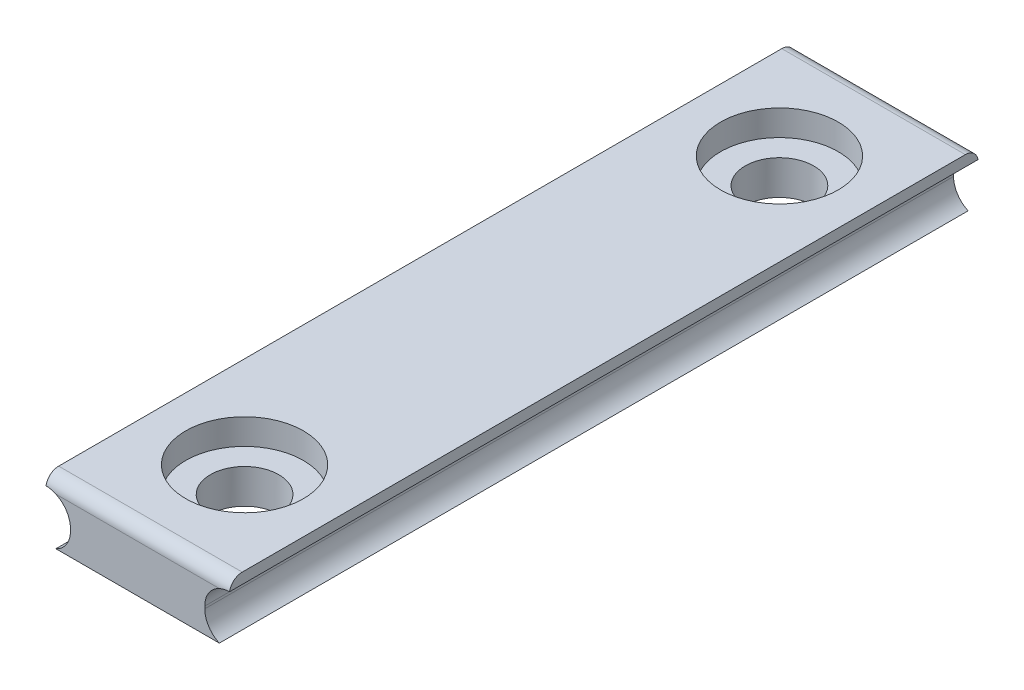
SolidWorks part; units mm, degrees
ref_plane "Front Plane" through (0, 0, 0) normal (0, 0, 1) x (1, 0, 0)
ref_plane "Top Plane" through (0, 0, 0) normal (0, 1, 0) x (1, 0, 0)
ref_plane "Right Plane" through (0, 0, 0) normal (1, 0, 0) x (0, 0, -1)
sketch "Sketch1" plane through (0, 0, 0) normal (0, 0, 1) x (1, 0, 0)
  line L0 (0, 0) -> (0, 2.8653) construction
  line L1 (0, 0) -> (3.9378, 0) construction
  line L2 (-3.14, 0.055) -> (-3.14, -0.055)
  line L3 (-4.29, 1.705) -> (4.29, 1.705)
  line L4 (-4.29, 1.705) -> (-4.29, 1.205)
  line L5 (-4.29, -1.705) -> (4.29, -1.705)
  line L6 (4.29, 1.705) -> (4.29, 1.205)
  line L7 (3.14, 0.055) -> (3.14, -0.055)
  line L8 (4.29, -1.205) -> (4.29, -1.705)
  line L9 (-4.29, -1.205) -> (-4.29, -1.705)
  arc A0 (3.14, 0.055) -> (4.29, 1.205) centre (4.29, 0.055) cw
  arc A1 (3.14, -0.055) -> (4.29, -1.205) centre (4.29, -0.055) ccw
  arc A2 (-3.14, 0.055) -> (-4.29, 1.205) centre (-4.29, 0.055) ccw
  arc A3 (-3.14, -0.055) -> (-4.29, -1.205) centre (-4.29, -0.055) cw
  dimension "D5" = 1.15
  dimension "D1" = 8.58
  dimension "D2" = 3.41
  dimension "D3" = 0.11
  dimension "D4" = 6.28
extrude "Boss-Extrude1" add sketch "Sketch1" along normal mid plane 35
sketch "Sketch2" plane through (0, 1.705, 0) normal (0, 1, 0) x (1, 0, 0)
  line L1 (0, 0) -> (0, 6.7591) construction
  line L2 (4.29, 17.5) -> (-4.29, 17.5) construction
  circle A0 centre (0, 12.5) radius 1.6
  dimension "D1" = 3.2
  dimension "D2" = 5
extrude "Cut-Extrude1" cut sketch "Sketch2" against normal through all
sketch "Sketch3" plane through (0, 1.705, 0) normal (0, 1, 0) x (1, 0, 0)
  circle A0 centre (0, 12.5) radius 2.75
  dimension "D1" = 5.5
extrude "Cut-Extrude2" cut sketch "Sketch3" against normal blind 1.2
mirror "Mirror1" about plane through (0, 0, 0) normal (0, 0, 1) of "Cut-Extrude2", "Cut-Extrude1"
sketch "Sketch4" plane through (0, -1.705, 0) normal (0, -1, 0) x (1, 0, 0)
  line L1 (-4.29, 17.5) -> (4.29, 17.5)
  line L2 (-4.29, 17.5) -> (-4.29, -17.5)
  line L3 (-4.29, -17.5) -> (4.29, -17.5)
  line L4 (4.29, 17.5) -> (4.29, -17.5)
extrude "Cut-Extrude3" cut sketch "Sketch4" against normal blind 0.6
fillet "Fillet1" radius 0.6 2 edges at (0, 1.705, -17.5) (0, 1.705, 17.5)
